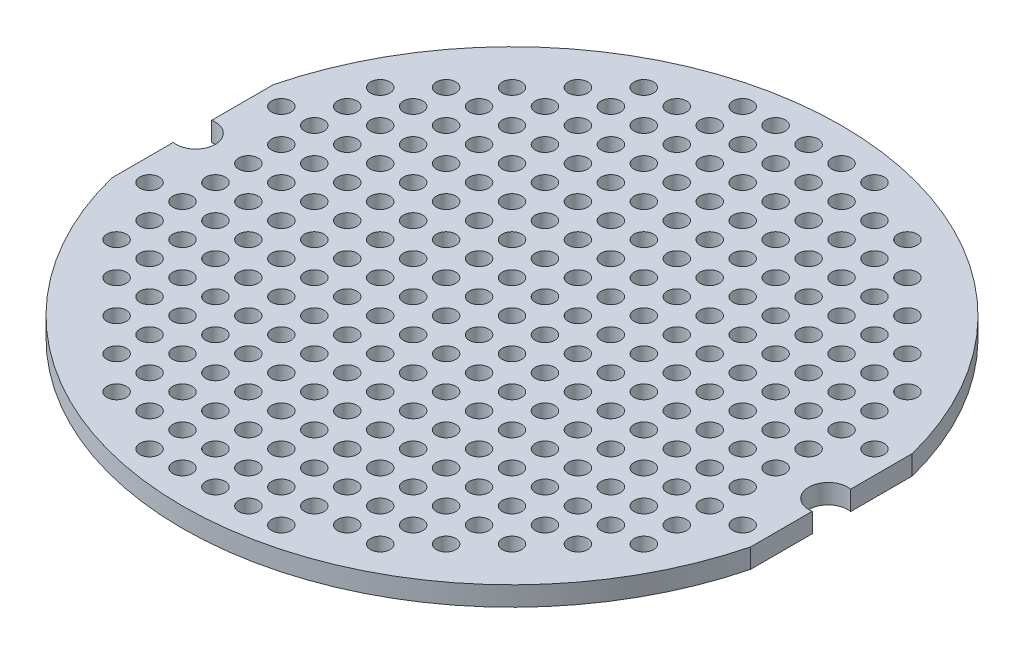
SolidWorks part; units mm, degrees
ref_plane "Front" through (0, 0, 0) normal (0, 0, 1) x (1, 0, 0)
ref_plane "Top" through (0, 0, 0) normal (0, 1, 0) x (1, 0, 0)
ref_plane "Right" through (0, 0, 0) normal (1, 0, 0) x (0, 0, -1)
sketch "ｽｹｯﾁ1" plane through (0, 0, 0) normal (0, 1, 0) x (1, 0, 0)
  circle A0 centre (0, 0) radius 25.4
  dimension "D1" = 50.8
extrude "ﾎﾞｽ - 押し出し1" add sketch "ｽｹｯﾁ1" along normal blind 1.5
sketch "ｽｹｯﾁ2" plane through (0, 1.5, 0) normal (0, 1, 0) x (1, 0, 0)
  line L0 (-25.4, 0) -> (25.4, 0) construction
  line L1 (0, 25.4) -> (0, -25.4) construction
  line L2 (-24.625, 6.2265) -> (-24.625, 1.479)
  line L3 (24.625, 6.2265) -> (24.625, 1.479)
  line L4 (-24.625, -1.479) -> (-24.625, -6.2265)
  line L5 (24.625, -1.479) -> (24.625, -6.2265)
  circle A0 centre (0, 0) radius 25.4 construction
  arc A1 (-24.625, -1.479) -> (-24.625, 1.479) centre (-24.375, 0) ccw
  arc A2 (24.625, -1.479) -> (24.625, 1.479) centre (24.375, 0) cw
  arc A3 (-24.625, 6.2265) -> (-24.625, -6.2265) centre (0, 0) ccw
  arc A4 (24.625, -6.2265) -> (25.3754, -1.1177) centre (0, 0) ccw
  arc A5 (25.3754, 1.1177) -> (24.625, 6.2265) centre (0, 0) ccw
  arc A6 (25.3754, 1.1177) -> (25.3754, -1.1177) centre (24.375, 0) cw
  dimension "D1" = 24.375
  dimension "D2" = 3
  dimension "D3" = 24.625
extrude "ｶｯﾄ - 押し出し1" cut sketch "ｽｹｯﾁ2" against normal through all
sketch "ｽｹｯﾁ3" plane through (0, 1.5, 0) normal (0, 1, 0) x (1, 0, 0)
  line L0 (22.86, 0) -> (-22.875, 0) construction
  line L1 (0, 25.4) -> (0, -25.4) construction
  circle A0 centre (-5.08, -22.86) radius 0.75
  circle A1 centre (-2.54, -22.86) radius 0.75
  circle A2 centre (0, 0) radius 0.75
  circle A3 centre (2.54, 0) radius 0.75
  circle A4 centre (5.08, 0) radius 0.75
  circle A5 centre (7.62, 0) radius 0.75
  circle A6 centre (10.16, 0) radius 0.75
  circle A7 centre (12.7, 0) radius 0.75
  circle A8 centre (15.24, 0) radius 0.75
  circle A9 centre (17.78, 0) radius 0.75
  circle A10 centre (20.32, 0) radius 0.75
  circle A12 centre (2.54, -2.54) radius 0.75
  circle A13 centre (5.08, -2.54) radius 0.75
  circle A14 centre (7.62, -2.54) radius 0.75
  circle A15 centre (10.16, -2.54) radius 0.75
  circle A16 centre (12.7, -2.54) radius 0.75
  circle A17 centre (15.24, -2.54) radius 0.75
  circle A18 centre (17.78, -2.54) radius 0.75
  circle A19 centre (20.32, -2.54) radius 0.75
  circle A21 centre (2.54, -5.08) radius 0.75
  circle A22 centre (5.08, -5.08) radius 0.75
  circle A23 centre (7.62, -5.08) radius 0.75
  circle A24 centre (10.16, -5.08) radius 0.75
  circle A25 centre (12.7, -5.08) radius 0.75
  circle A26 centre (15.24, -5.08) radius 0.75
  circle A27 centre (17.78, -5.08) radius 0.75
  circle A28 centre (20.32, -5.08) radius 0.75
  circle A29 centre (22.86, -5.08) radius 0.75
  circle A30 centre (2.54, -7.62) radius 0.75
  circle A31 centre (5.08, -7.62) radius 0.75
  circle A32 centre (7.62, -7.62) radius 0.75
  circle A33 centre (10.16, -7.62) radius 0.75
  circle A34 centre (12.7, -7.62) radius 0.75
  circle A35 centre (15.24, -7.62) radius 0.75
  circle A36 centre (17.78, -7.62) radius 0.75
  circle A37 centre (20.32, -7.62) radius 0.75
  circle A39 centre (2.54, -10.16) radius 0.75
  circle A40 centre (5.08, -10.16) radius 0.75
  circle A41 centre (7.62, -10.16) radius 0.75
  circle A42 centre (10.16, -10.16) radius 0.75
  circle A43 centre (12.7, -10.16) radius 0.75
  circle A44 centre (15.24, -10.16) radius 0.75
  circle A45 centre (17.78, -10.16) radius 0.75
  circle A46 centre (20.32, -10.16) radius 0.75
  circle A48 centre (2.54, -12.7) radius 0.75
  circle A49 centre (5.08, -12.7) radius 0.75
  circle A50 centre (7.62, -12.7) radius 0.75
  circle A51 centre (10.16, -12.7) radius 0.75
  circle A52 centre (12.7, -12.7) radius 0.75
  circle A53 centre (15.24, -12.7) radius 0.75
  circle A54 centre (17.78, -12.7) radius 0.75
  circle A57 centre (2.54, -15.24) radius 0.75
  circle A58 centre (5.08, -15.24) radius 0.75
  circle A59 centre (7.62, -15.24) radius 0.75
  circle A60 centre (10.16, -15.24) radius 0.75
  circle A61 centre (12.7, -15.24) radius 0.75
  circle A62 centre (15.24, -15.24) radius 0.75
  circle A66 centre (2.54, -17.78) radius 0.75
  circle A67 centre (5.08, -17.78) radius 0.75
  circle A68 centre (7.62, -17.78) radius 0.75
  circle A69 centre (10.16, -17.78) radius 0.75
  circle A70 centre (12.7, -17.78) radius 0.75
  circle A75 centre (2.54, -20.32) radius 0.75
  circle A76 centre (5.08, -20.32) radius 0.75
  circle A77 centre (7.62, -20.32) radius 0.75
  circle A78 centre (10.16, -20.32) radius 0.75
  circle A84 centre (2.54, -22.86) radius 0.75
  circle A85 centre (5.08, -22.86) radius 0.75
  circle A93 centre (0, -2.54) radius 0.75
  circle A94 centre (0, -5.08) radius 0.75
  circle A95 centre (0, -7.62) radius 0.75
  circle A96 centre (0, -10.16) radius 0.75
  circle A97 centre (0, -12.7) radius 0.75
  circle A98 centre (0, -15.24) radius 0.75
  circle A99 centre (0, -17.78) radius 0.75
  circle A100 centre (0, -20.32) radius 0.75
  circle A101 centre (0, -22.86) radius 0.75
  circle A102 centre (20.32, -15.24) radius 0.75 [skipped]
  circle A103 centre (22.86, -15.24) radius 0.75 [skipped]
  circle A104 centre (20.32, -17.78) radius 0.75 [skipped]
  circle A105 centre (22.86, -17.78) radius 0.75 [skipped]
  circle A106 centre (20.32, -20.32) radius 0.75 [skipped]
  circle A107 centre (22.86, -20.32) radius 0.75 [skipped]
  circle A108 centre (20.32, -22.86) radius 0.75 [skipped]
  circle A109 centre (22.86, -22.86) radius 0.75 [skipped]
  circle A110 centre (22.86, 0) radius 0.75 [skipped]
  circle A111 centre (22.86, -2.54) radius 0.75 [skipped]
  circle A112 centre (22.86, -7.62) radius 0.75 [skipped]
  circle A113 centre (22.86, -10.16) radius 0.75 [skipped]
  circle A114 centre (22.86, -12.7) radius 0.75 [skipped]
  circle A115 centre (20.32, -12.7) radius 0.75 [skipped]
  circle A116 centre (17.78, -15.24) radius 0.75 [skipped]
  circle A117 centre (15.24, -17.78) radius 0.75 [skipped]
  circle A118 centre (17.78, -17.78) radius 0.75 [skipped]
  circle A119 centre (15.24, -20.32) radius 0.75 [skipped]
  circle A120 centre (17.78, -20.32) radius 0.75 [skipped]
  circle A121 centre (15.24, -22.86) radius 0.75 [skipped]
  circle A122 centre (17.78, -22.86) radius 0.75 [skipped]
  circle A123 centre (12.7, -20.32) radius 0.75 [skipped]
  circle A124 centre (12.7, -22.86) radius 0.75 [skipped]
  circle A125 centre (10.16, -22.86) radius 0.75 [skipped]
  circle A126 centre (7.62, -22.86) radius 0.75 [skipped]
  arc A127 (-24.625, -1.479) -> (-24.625, 1.479) centre (-24.375, 0) ccw construction
  arc A128 (24.625, 6.2265) -> (-24.625, 6.2265) centre (0, 0) ccw construction
  arc A129 (-24.625, -6.2265) -> (24.625, -6.2265) centre (0, 0) ccw construction
  circle A130 centre (-10.16, -20.32) radius 0.75
  circle A131 centre (-7.62, -20.32) radius 0.75
  circle A132 centre (-5.08, -20.32) radius 0.75
  circle A133 centre (-2.54, -20.32) radius 0.75
  circle A134 centre (-12.7, -17.78) radius 0.75
  circle A135 centre (-10.16, -17.78) radius 0.75
  circle A136 centre (-7.62, -17.78) radius 0.75
  circle A137 centre (-5.08, -17.78) radius 0.75
  circle A138 centre (-2.54, -17.78) radius 0.75
  circle A139 centre (-15.24, -15.24) radius 0.75
  circle A140 centre (-12.7, -15.24) radius 0.75
  circle A141 centre (-10.16, -15.24) radius 0.75
  circle A142 centre (-7.62, -15.24) radius 0.75
  circle A143 centre (-5.08, -15.24) radius 0.75
  circle A144 centre (-2.54, -15.24) radius 0.75
  circle A145 centre (-17.78, -12.7) radius 0.75
  circle A146 centre (-15.24, -12.7) radius 0.75
  circle A147 centre (-12.7, -12.7) radius 0.75
  circle A148 centre (-10.16, -12.7) radius 0.75
  circle A149 centre (-7.62, -12.7) radius 0.75
  circle A150 centre (-5.08, -12.7) radius 0.75
  circle A151 centre (-2.54, -12.7) radius 0.75
  circle A152 centre (-20.32, -10.16) radius 0.75
  circle A153 centre (-17.78, -10.16) radius 0.75
  circle A154 centre (-15.24, -10.16) radius 0.75
  circle A155 centre (-12.7, -10.16) radius 0.75
  circle A156 centre (-10.16, -10.16) radius 0.75
  circle A157 centre (-7.62, -10.16) radius 0.75
  circle A158 centre (-5.08, -10.16) radius 0.75
  circle A159 centre (-2.54, -10.16) radius 0.75
  circle A160 centre (-20.32, -7.62) radius 0.75
  circle A161 centre (-17.78, -7.62) radius 0.75
  circle A162 centre (-15.24, -7.62) radius 0.75
  circle A163 centre (-12.7, -7.62) radius 0.75
  circle A164 centre (-10.16, -7.62) radius 0.75
  circle A165 centre (-7.62, -7.62) radius 0.75
  circle A166 centre (-5.08, -7.62) radius 0.75
  circle A167 centre (-2.54, -7.62) radius 0.75
  circle A168 centre (-22.86, -5.08) radius 0.75
  circle A169 centre (-20.32, -5.08) radius 0.75
  circle A170 centre (-17.78, -5.08) radius 0.75
  circle A171 centre (-15.24, -5.08) radius 0.75
  circle A172 centre (-12.7, -5.08) radius 0.75
  circle A173 centre (-10.16, -5.08) radius 0.75
  circle A174 centre (-7.62, -5.08) radius 0.75
  circle A175 centre (-5.08, -5.08) radius 0.75
  circle A176 centre (-2.54, -5.08) radius 0.75
  circle A177 centre (-20.32, -2.54) radius 0.75
  circle A178 centre (-17.78, -2.54) radius 0.75
  circle A179 centre (-15.24, -2.54) radius 0.75
  circle A180 centre (-12.7, -2.54) radius 0.75
  circle A181 centre (-10.16, -2.54) radius 0.75
  circle A182 centre (-7.62, -2.54) radius 0.75
  circle A183 centre (-5.08, -2.54) radius 0.75
  circle A184 centre (-2.54, -2.54) radius 0.75
  circle A185 centre (-20.32, 0) radius 0.75
  circle A186 centre (-17.78, 0) radius 0.75
  circle A187 centre (-15.24, 0) radius 0.75
  circle A188 centre (-12.7, 0) radius 0.75
  circle A189 centre (-10.16, 0) radius 0.75
  circle A190 centre (-7.62, 0) radius 0.75
  circle A191 centre (-5.08, 0) radius 0.75
  circle A192 centre (-2.54, 0) radius 0.75
  circle A193 centre (-2.54, 2.54) radius 0.75
  circle A194 centre (-5.08, 2.54) radius 0.75
  circle A195 centre (-7.62, 2.54) radius 0.75
  circle A196 centre (-10.16, 2.54) radius 0.75
  circle A197 centre (-12.7, 2.54) radius 0.75
  circle A198 centre (-15.24, 2.54) radius 0.75
  circle A199 centre (-17.78, 2.54) radius 0.75
  circle A200 centre (-20.32, 2.54) radius 0.75
  circle A201 centre (-2.54, 5.08) radius 0.75
  circle A202 centre (-5.08, 5.08) radius 0.75
  circle A203 centre (-7.62, 5.08) radius 0.75
  circle A204 centre (-10.16, 5.08) radius 0.75
  circle A205 centre (-12.7, 5.08) radius 0.75
  circle A206 centre (-15.24, 5.08) radius 0.75
  circle A207 centre (-17.78, 5.08) radius 0.75
  circle A208 centre (-20.32, 5.08) radius 0.75
  circle A209 centre (-22.86, 5.08) radius 0.75
  circle A210 centre (-2.54, 7.62) radius 0.75
  circle A211 centre (-5.08, 7.62) radius 0.75
  circle A212 centre (-7.62, 7.62) radius 0.75
  circle A213 centre (-10.16, 7.62) radius 0.75
  circle A214 centre (-12.7, 7.62) radius 0.75
  circle A215 centre (-15.24, 7.62) radius 0.75
  circle A216 centre (-17.78, 7.62) radius 0.75
  circle A217 centre (-20.32, 7.62) radius 0.75
  circle A218 centre (-2.54, 10.16) radius 0.75
  circle A219 centre (-5.08, 10.16) radius 0.75
  circle A220 centre (-7.62, 10.16) radius 0.75
  circle A221 centre (-10.16, 10.16) radius 0.75
  circle A222 centre (-12.7, 10.16) radius 0.75
  circle A223 centre (-15.24, 10.16) radius 0.75
  circle A224 centre (-17.78, 10.16) radius 0.75
  circle A225 centre (-20.32, 10.16) radius 0.75
  circle A226 centre (-2.54, 12.7) radius 0.75
  circle A227 centre (-5.08, 12.7) radius 0.75
  circle A228 centre (-7.62, 12.7) radius 0.75
  circle A229 centre (-10.16, 12.7) radius 0.75
  circle A230 centre (-12.7, 12.7) radius 0.75
  circle A231 centre (-15.24, 12.7) radius 0.75
  circle A232 centre (-17.78, 12.7) radius 0.75
  circle A233 centre (-2.54, 15.24) radius 0.75
  circle A234 centre (-5.08, 15.24) radius 0.75
  circle A235 centre (-7.62, 15.24) radius 0.75
  circle A236 centre (-10.16, 15.24) radius 0.75
  circle A237 centre (-12.7, 15.24) radius 0.75
  circle A238 centre (-15.24, 15.24) radius 0.75
  circle A239 centre (-2.54, 17.78) radius 0.75
  circle A240 centre (-5.08, 17.78) radius 0.75
  circle A241 centre (-7.62, 17.78) radius 0.75
  circle A242 centre (-10.16, 17.78) radius 0.75
  circle A243 centre (-12.7, 17.78) radius 0.75
  circle A244 centre (-2.54, 20.32) radius 0.75
  circle A245 centre (-5.08, 20.32) radius 0.75
  circle A246 centre (-7.62, 20.32) radius 0.75
  circle A247 centre (-10.16, 20.32) radius 0.75
  circle A248 centre (0, 22.86) radius 0.75
  circle A249 centre (0, 20.32) radius 0.75
  circle A250 centre (0, 17.78) radius 0.75
  circle A251 centre (0, 15.24) radius 0.75
  circle A252 centre (0, 12.7) radius 0.75
  circle A253 centre (0, 10.16) radius 0.75
  circle A254 centre (0, 7.62) radius 0.75
  circle A255 centre (0, 5.08) radius 0.75
  circle A256 centre (0, 2.54) radius 0.75
  circle A257 centre (5.08, 22.86) radius 0.75
  circle A258 centre (2.54, 22.86) radius 0.75
  circle A259 centre (10.16, 20.32) radius 0.75
  circle A260 centre (7.62, 20.32) radius 0.75
  circle A261 centre (5.08, 20.32) radius 0.75
  circle A262 centre (2.54, 20.32) radius 0.75
  circle A263 centre (12.7, 17.78) radius 0.75
  circle A264 centre (10.16, 17.78) radius 0.75
  circle A265 centre (7.62, 17.78) radius 0.75
  circle A266 centre (5.08, 17.78) radius 0.75
  circle A267 centre (2.54, 17.78) radius 0.75
  circle A268 centre (15.24, 15.24) radius 0.75
  circle A269 centre (12.7, 15.24) radius 0.75
  circle A270 centre (10.16, 15.24) radius 0.75
  circle A271 centre (7.62, 15.24) radius 0.75
  circle A272 centre (5.08, 15.24) radius 0.75
  circle A273 centre (2.54, 15.24) radius 0.75
  circle A274 centre (17.78, 12.7) radius 0.75
  circle A275 centre (15.24, 12.7) radius 0.75
  circle A276 centre (12.7, 12.7) radius 0.75
  circle A277 centre (10.16, 12.7) radius 0.75
  circle A278 centre (7.62, 12.7) radius 0.75
  circle A279 centre (5.08, 12.7) radius 0.75
  circle A280 centre (2.54, 12.7) radius 0.75
  circle A281 centre (20.32, 10.16) radius 0.75
  circle A282 centre (17.78, 10.16) radius 0.75
  circle A283 centre (15.24, 10.16) radius 0.75
  circle A284 centre (12.7, 10.16) radius 0.75
  circle A285 centre (10.16, 10.16) radius 0.75
  circle A286 centre (7.62, 10.16) radius 0.75
  circle A287 centre (5.08, 10.16) radius 0.75
  circle A288 centre (2.54, 10.16) radius 0.75
  circle A289 centre (20.32, 7.62) radius 0.75
  circle A290 centre (17.78, 7.62) radius 0.75
  circle A291 centre (15.24, 7.62) radius 0.75
  circle A292 centre (12.7, 7.62) radius 0.75
  circle A293 centre (10.16, 7.62) radius 0.75
  circle A294 centre (7.62, 7.62) radius 0.75
  circle A295 centre (5.08, 7.62) radius 0.75
  circle A296 centre (2.54, 7.62) radius 0.75
  circle A297 centre (22.86, 5.08) radius 0.75
  circle A298 centre (20.32, 5.08) radius 0.75
  circle A299 centre (17.78, 5.08) radius 0.75
  circle A300 centre (15.24, 5.08) radius 0.75
  circle A301 centre (12.7, 5.08) radius 0.75
  circle A302 centre (10.16, 5.08) radius 0.75
  circle A303 centre (7.62, 5.08) radius 0.75
  circle A304 centre (5.08, 5.08) radius 0.75
  circle A305 centre (2.54, 5.08) radius 0.75
  circle A306 centre (20.32, 2.54) radius 0.75
  circle A307 centre (17.78, 2.54) radius 0.75
  circle A308 centre (15.24, 2.54) radius 0.75
  circle A309 centre (12.7, 2.54) radius 0.75
  circle A310 centre (10.16, 2.54) radius 0.75
  circle A311 centre (7.62, 2.54) radius 0.75
  circle A312 centre (5.08, 2.54) radius 0.75
  circle A313 centre (2.54, 2.54) radius 0.75
  circle A314 centre (-2.54, 22.86) radius 0.75
  circle A315 centre (-5.08, 22.86) radius 0.75
  dimension "D1" = 1.5
  dimension "D2" = 10
  dimension "D3" = 10
extrude "ｶｯﾄ - 押し出し2" cut sketch "ｽｹｯﾁ3" against normal through all
